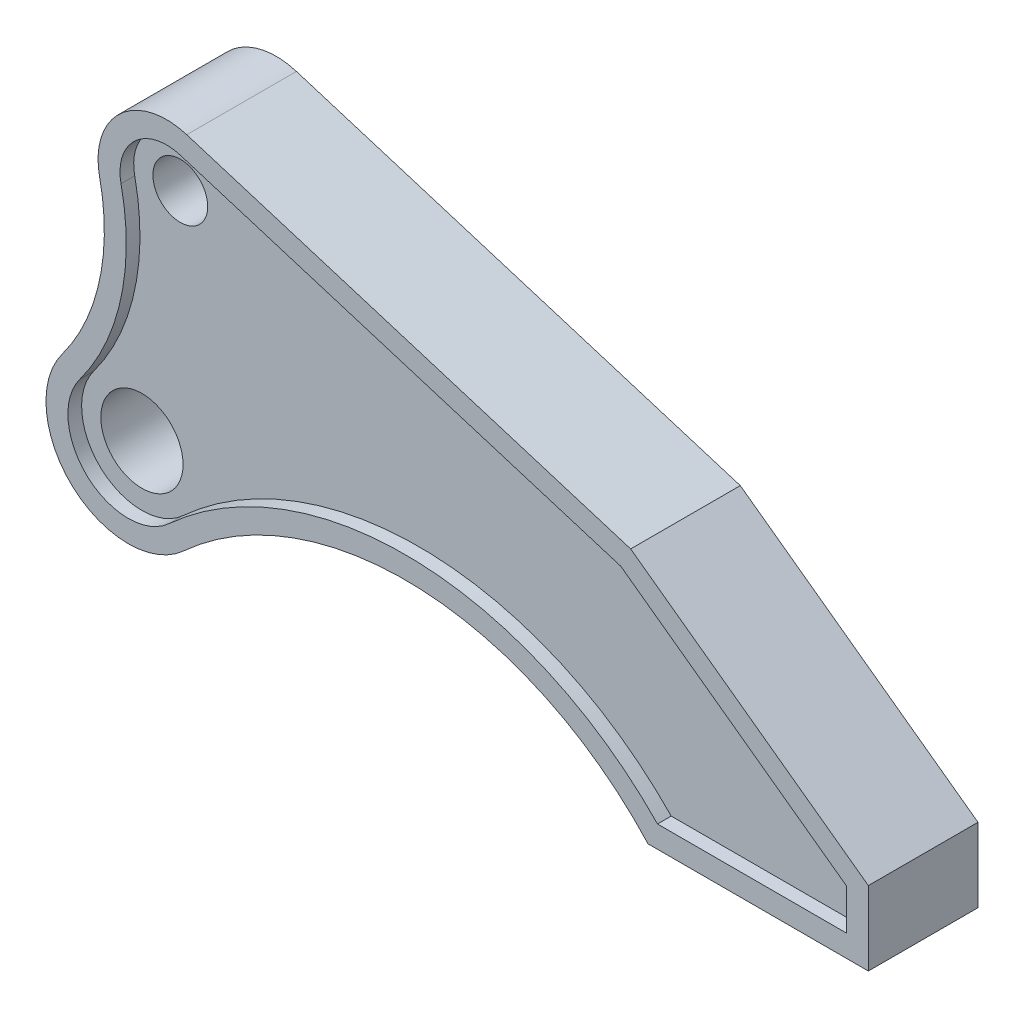
SolidWorks part; units mm, degrees
ref_plane "Front Plane" through (0, 0, 0) normal (0, 0, 1) x (1, 0, 0)
ref_plane "Top Plane" through (0, 0, 0) normal (0, 1, 0) x (1, 0, 0)
ref_plane "Right Plane" through (0, 0, 0) normal (1, 0, 0) x (0, 0, -1)
sketch "Sketch2" plane through (0, 0, 0) normal (0, 0, 1) x (1, 0, 0)
  line L0 (21.3613, 109.8917) -> (183.2879, 60)
  line L1 (183.2879, 60) -> (270, -3)
  line L2 (270, -3) -> (270, -30)
  line L3 (270, -30) -> (189.6287, -30)
  circle A0 centre (0, 0) radius 30
  circle A1 centre (14, 86) radius 25
  arc A2 (-10.4435, 80.7545) -> (-24.0853, 17.8857) centre (-86.7072, 64.3884) cw
  arc A3 (20.2, -22.1802) -> (189.6287, -30) centre (101, -110.9009) cw
  point P15 (0, 0)
  point P16 (0, 0)
  dimension "D1" = 60
  dimension "D2" = 50
  dimension "D4" = 14
  dimension "D5" = 78
  dimension "D8" = 120
  dimension "D9" = 101
  dimension "D3" = 86
  dimension "D6" = 90
  dimension "D7" = 27
  dimension "270" = 270
  dimension "D10" = 36
extrude "Boss-Extrude1" add sketch "Sketch2" along normal mid plane 30 contours A0 A3 L3 L2 L1 L0 A1 A2 | A0 | A1
sketch "Sketch4" plane through (0, 0, 0) normal (0, 0, 1) x (1, 0, 0)
  line L8 (193.0904, -22) -> (262, -22)
  line L9 (262, -22) -> (262, -7.0762)
  line L10 (262, -7.0762) -> (179.6615, 52.7462)
  line L11 (179.6615, 52.7462) -> (19.0057, 102.2463)
  line L12 (193.0904, -22) -> (262, -22)
  line L13 (262, -22) -> (262, -7.0762)
  line L14 (262, -7.0762) -> (179.6615, 52.7462)
  line L15 (179.6615, 52.7462) -> (19.0057, 102.2463)
  line L16 (189.6287, -30) -> (270, -30)
  line L17 (270, -30) -> (270, -3)
  line L18 (270, -3) -> (183.2879, 60)
  line L19 (183.2879, 60) -> (21.3613, 109.8917)
  line L20 (189.6287, -30) -> (270, -30)
  line L21 (270, -30) -> (270, -3)
  line L22 (270, -3) -> (183.2879, 60)
  line L23 (183.2879, 60) -> (21.3613, 109.8917)
  arc A8 (-17.6626, 13.1162) -> (-2.6216, 82.433) centre (-86.7072, 64.3884) ccw
  arc A9 (-17.6626, 13.1162) -> (14.8133, -16.2655) centre (0, 0) ccw
  arc A10 (193.0904, -22) -> (14.8133, -16.2655) centre (101, -110.9009) ccw
  arc A11 (19.0057, 102.2463) -> (-2.6216, 82.433) centre (14, 86) ccw
  arc A12 (-17.6626, 13.1162) -> (-2.6216, 82.433) centre (-86.7072, 64.3884) ccw
  arc A13 (-17.6626, 13.1162) -> (14.8133, -16.2655) centre (0, 0) ccw
  arc A14 (193.0904, -22) -> (14.8133, -16.2655) centre (101, -110.9009) ccw
  arc A15 (19.0057, 102.2463) -> (-2.6216, 82.433) centre (14, 86) ccw
  arc A16 (-24.0853, 17.8857) -> (-10.4435, 80.7545) centre (-86.7072, 64.3884) ccw
  arc A17 (-24.0853, 17.8857) -> (20.2, -22.1802) centre (0, 0) ccw
  arc A18 (189.6287, -30) -> (20.2, -22.1802) centre (101, -110.9009) ccw
  arc A19 (21.3613, 109.8917) -> (-10.4435, 80.7545) centre (14, 86) ccw
  arc A20 (-24.0853, 17.8857) -> (-10.4435, 80.7545) centre (-86.7072, 64.3884) ccw
  arc A21 (-24.0853, 17.8857) -> (20.2, -22.1802) centre (0, 0) ccw
  arc A22 (189.6287, -30) -> (20.2, -22.1802) centre (101, -110.9009) ccw
  arc A23 (21.3613, 109.8917) -> (-10.4435, 80.7545) centre (14, 86) ccw
  dimension "D1" = 8
  dimension "D2" = 0
extrude "Boss-Extrude2" add sketch "Sketch4" along normal mid plane 40
sketch "Sketch5" plane through (0, 0, 15) normal (0, 0, 1) x (1, 0, 0)
  circle A0 centre (14, 86) radius 10
  circle A1 centre (0, 0) radius 15
  dimension "D1" = 20
  dimension "D2" = 30
  dimension "D3" = 86
  dimension "D4" = 14
extrude "Cut-Extrude2" cut sketch "Sketch5" against normal blind 40
